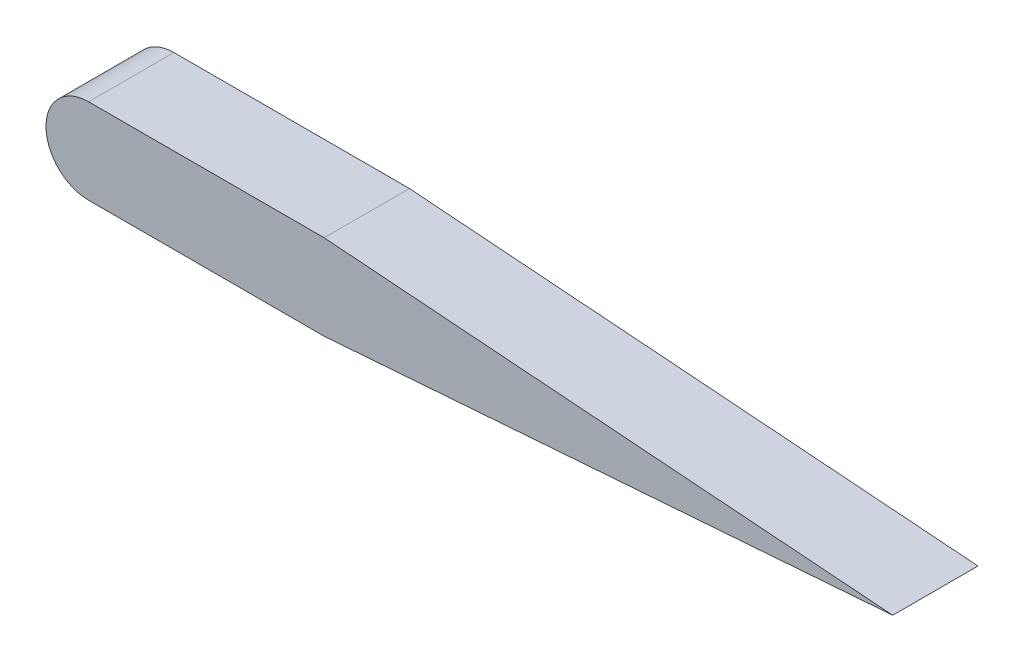
SolidWorks part; units mm, degrees
ref_plane "Front Plane" through (0, 0, 0) normal (0, 0, 1) x (1, 0, 0)
ref_plane "Top Plane" through (0, 0, 0) normal (0, 1, 0) x (1, 0, 0)
ref_plane "Right Plane" through (0, 0, 0) normal (1, 0, 0) x (0, 0, -1)
sketch "Sketch1" plane through (0, 0, 0) normal (0, 0, 1) x (1, 0, 0)
  line L3 (4.2333, 1.5875) -> (25.4, 0)
  line L4 (4.2333, -1.5875) -> (25.4, 0)
  line L5 (-4.5337, 1.5875) -> (4.2333, 1.5875)
  line L6 (-4.5337, -1.5875) -> (4.2333, -1.5875)
  line L7 (0, 1.5875) -> (0, 1.905)
  arc A2 (-4.5337, 1.5875) -> (-4.5337, -1.5875) centre (-4.5337, 0) ccw
  point P7 (0, 0)
  dimension "D4" = 3.175
extrude "Boss-Extrude1" add sketch "Sketch1" along normal blind 3.175 contours L5 A2 L6 L4 L3
